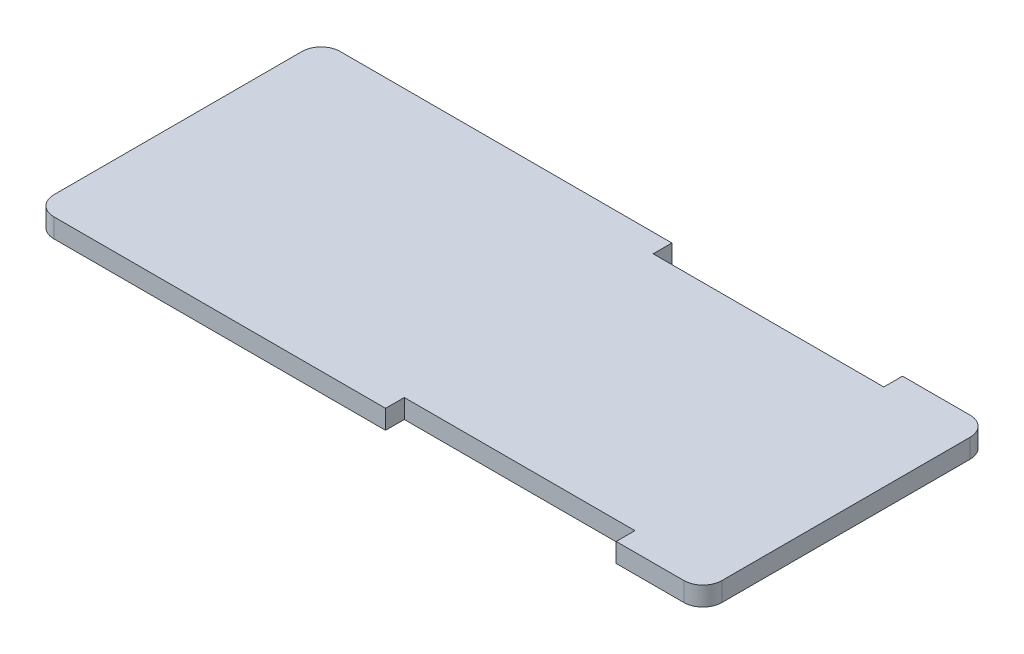
SolidWorks part; units mm, degrees
ref_plane "Front Plane" through (0, 0, 0) normal (0, 0, 1) x (1, 0, 0)
ref_plane "Top Plane" through (0, 0, 0) normal (0, 1, 0) x (1, 0, 0)
ref_plane "Right Plane" through (0, 0, 0) normal (1, 0, 0) x (0, 0, -1)
sketch "Sketch1" plane through (0, 0, 0) normal (0, 1, 0) x (1, 0, 0)
  line L1 (0, 0) -> (350, 0)
  line L2 (0, 0) -> (0, -150)
  line L3 (0, -150) -> (350, -150)
  line L4 (350, 0) -> (350, -150)
  dimension "D1" = 350
  dimension "D2" = 150
extrude "Boss-Extrude1" add sketch "Sketch1" along normal blind 10
sketch "Sketch2" plane through (0, 10, 0) normal (0, 1, 0) x (1, 0, 0)
  line L0 (175, 0) -> (175, -92.2262) construction
  line L1 (350, 0) -> (0, 0) construction
  line L2 (0, -75) -> (350, -75) construction
  line L3 (0, 0) -> (0, -150) construction
  line L4 (350, -150) -> (350, 0) construction
sketch "Sketch3" plane through (0, 10, 0) normal (0, 1, 0) x (1, 0, 0)
  line L0 (350, 0) -> (0, 0) construction
  line L1 (47.2687, 0) -> (172.2687, 0)
  line L2 (47.2687, 0) -> (47.2687, -12.849) construction
  line L3 (47.2687, -12.849) -> (172.2687, -12.849) construction
  line L4 (172.2687, 0) -> (172.2687, -12.849)
  line L5 (175, 0) -> (175, -92.2262)
  line L6 (0, -75) -> (350, -75)
  line L7 (47.2687, -137.151) -> (172.2687, -137.151) construction
  line L8 (172.2687, -150) -> (172.2687, -137.151)
  line L9 (47.2687, -150) -> (172.2687, -150)
  line L10 (47.2687, -150) -> (47.2687, -137.151) construction
  line L11 (302.7313, -150) -> (302.7313, -137.151) construction
  line L12 (302.7313, -150) -> (177.7313, -150)
  line L13 (177.7313, -150) -> (177.7313, -137.151)
  line L14 (302.7313, -137.151) -> (177.7313, -137.151) construction
  line L15 (302.7313, -12.849) -> (177.7313, -12.849) construction
  line L16 (177.7313, 0) -> (177.7313, -12.849)
  line L17 (302.7313, 0) -> (177.7313, 0)
  line L18 (302.7313, 0) -> (302.7313, -12.849) construction
  dimension "D1" = 125
fillet "Fillet2" radius 10 4 edges at (0, 5, 0) (0, 5, 150) (350, 5, 0) (350, 5, 150)
sketch "Sketch9" plane through (0, 10, 0) normal (0, 1, 0) x (1, 0, 0)
  line L0 (10, -150) -> (340, -150) construction
  line L1 (304.5814, -150) -> (183.7603, -150)
  line L2 (304.5814, -150) -> (304.5814, -140.1832)
  line L3 (304.5814, -140.1832) -> (183.7603, -140.1832)
  line L4 (183.7603, -150) -> (183.7603, -140.1832)
  line L5 (350, -75) -> (222.5267, -75)
  line L6 (304.5814, -9.8168) -> (183.7603, -9.8168)
  line L7 (183.7603, 0) -> (183.7603, -9.8168)
  line L8 (304.5814, 0) -> (183.7603, 0)
  line L9 (304.5814, 0) -> (304.5814, -9.8168)
  line M14 (10, -150) -> (340, -150)
  line M18 (340, 0) -> (10, 0)
extrude "Cut-Extrude6" cut sketch "Sketch9" against normal blind 25 contours L4 L2 L3 M14 | L9 L7 L6 M18
